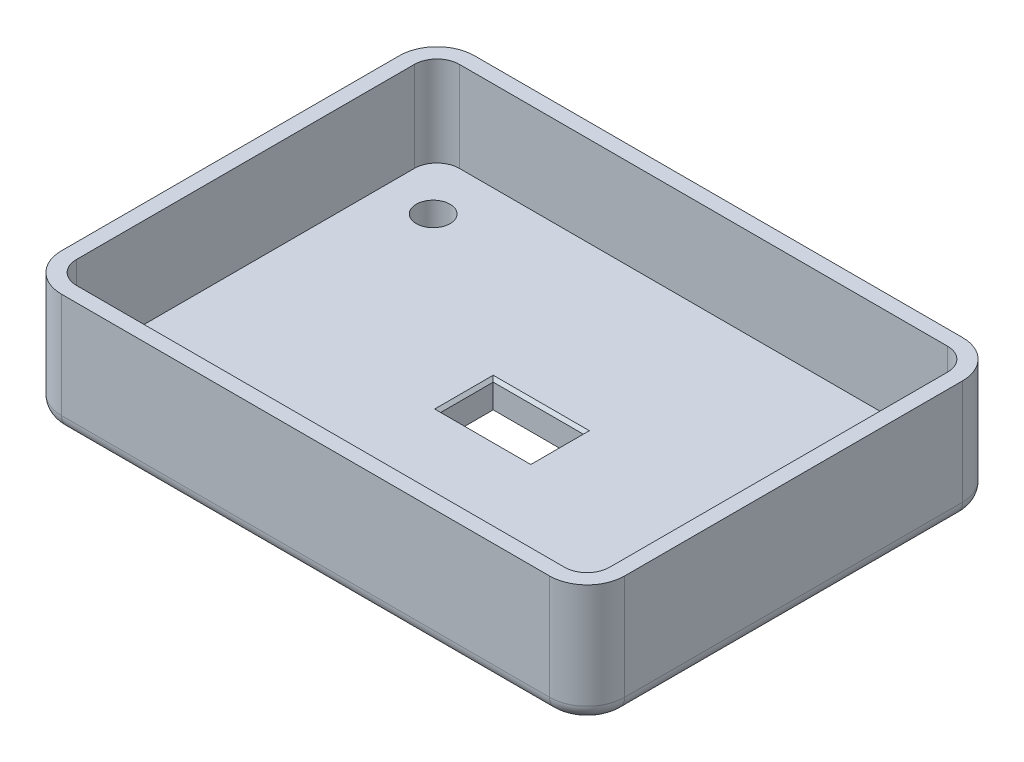
SolidWorks part; units mm, degrees
ref_plane "Front Plane" through (0, 0, 0) normal (0, 0, 1) x (1, 0, 0)
ref_plane "Top Plane" through (0, 0, 0) normal (0, 1, 0) x (1, 0, 0)
ref_plane "Right Plane" through (0, 0, 0) normal (1, 0, 0) x (0, 0, -1)
sketch "Sketch1" plane through (0, 0, 0) normal (0, 1, 0) x (1, 0, 0)
  line L1 (-37.5, -27.5) -> (37.5, -27.5)
  line L2 (-37.5, -27.5) -> (-37.5, 27.5)
  line L3 (-37.5, 27.5) -> (37.5, 27.5)
  line L4 (37.5, -27.5) -> (37.5, 27.5)
  line L5 (-37.5, -27.5) -> (37.5, 27.5) construction
  line L6 (-37.5, 27.5) -> (37.5, -27.5) construction
  point P0 (0, 0)
  dimension "D1" = 75
  dimension "D2" = 55
extrude "Boss-Extrude1" add sketch "Sketch1" along normal blind 4
sketch "Sketch2" plane through (0, 4, 0) normal (0, 1, 0) x (1, 0, 0)
  line L1 (-37.5, -27.5) -> (37.5, -27.5)
  line L2 (-37.5, -27.5) -> (-37.5, 27.5)
  line L3 (-37.5, 27.5) -> (37.5, 27.5)
  line L4 (37.5, -27.5) -> (37.5, 27.5)
  line L5 (-37.5, -27.5) -> (37.5, 27.5) construction
  line L6 (-37.5, 27.5) -> (37.5, -27.5) construction
  line L7 (-35.5, -25.5) -> (35.5, -25.5)
  line L8 (-35.5, -25.5) -> (-35.5, 25.5)
  line L9 (-35.5, 25.5) -> (35.5, 25.5)
  line L10 (35.5, -25.5) -> (35.5, 25.5)
  line L11 (-35.5, -25.5) -> (35.5, 25.5) construction
  line L12 (-35.5, 25.5) -> (35.5, -25.5) construction
  point P0 (0, 0)
  point P7 (0, 0)
  dimension "D1" = 2
  dimension "D2" = 2
extrude "Boss-Extrude2" add sketch "Sketch2" along normal blind 12
sketch "Sketch3" plane through (0, 4, 0) normal (0, 1, 0) x (1, 0, 0)
  line L1 (-29, -18.5) -> (29, -18.5) construction
  line L2 (-29, -18.5) -> (-29, 18.5) construction
  line L3 (-29, 18.5) -> (29, 18.5) construction
  line L4 (29, -18.5) -> (29, 18.5) construction
  line L5 (-29, -18.5) -> (29, 18.5) construction
  line L6 (-29, 18.5) -> (29, -18.5) construction
  line L7 (-6, -3.5) -> (6, -3.5)
  line L8 (-6, -3.5) -> (-6, 3.5)
  line L9 (-6, 3.5) -> (6, 3.5)
  line L10 (6, -3.5) -> (6, 3.5)
  line L11 (-6, -3.5) -> (6, 3.5) construction
  line L12 (-6, 3.5) -> (6, -3.5) construction
  circle A0 centre (-29, 18.5) radius 2.25
  circle A1 centre (29, 18.5) radius 2.25
  circle A2 centre (29, -18.5) radius 2.25
  circle A3 centre (-29, -18.5) radius 2.25
  point P0 (0, 0)
  point P10 (0, 0)
  dimension "D3" = 4.5
  dimension "D4" = 12
  dimension "D1" = 58
  dimension "D2" = 37
  dimension "D5" = 7
extrude "Cut-Extrude1" cut sketch "Sketch3" against normal through all
fillet "Fillet1" radius 5 4 edges at (-37.5, 8, -27.5) (37.5, 8, -27.5) (37.5, 8, 27.5) (-37.5, 8, 27.5)
fillet "Fillet2" radius 3 4 edges at (-35.5, 10, -25.5) (-35.5, 10, 25.5) (35.5, 10, 25.5) (35.5, 10, -25.5)
fillet "Fillet3" radius 2 8 edges at (36.0355, 0, -26.0355) (37.5, 0, 0) (36.0355, 0, 26.0355) (0, 0, 27.5) (-36.0355, 0, 26.0355) (-37.5, 0, 0) (-36.0355, 0, -26.0355) (0, 0, -27.5)
chamfer "Chamfer1" distance 0.4 angle 45 12 edges at (29, 0, -16.25) (29, 0, 20.75) (-29, 0, 20.75) (-29, 0, -16.25) (6, 0, 0) (0, 0, 3.5) (-6, 0, 0) (0, 0, -3.5) (0, 4, 3.5) (6, 4, 0) (-6, 4, 0) (0, 4, -3.5)
